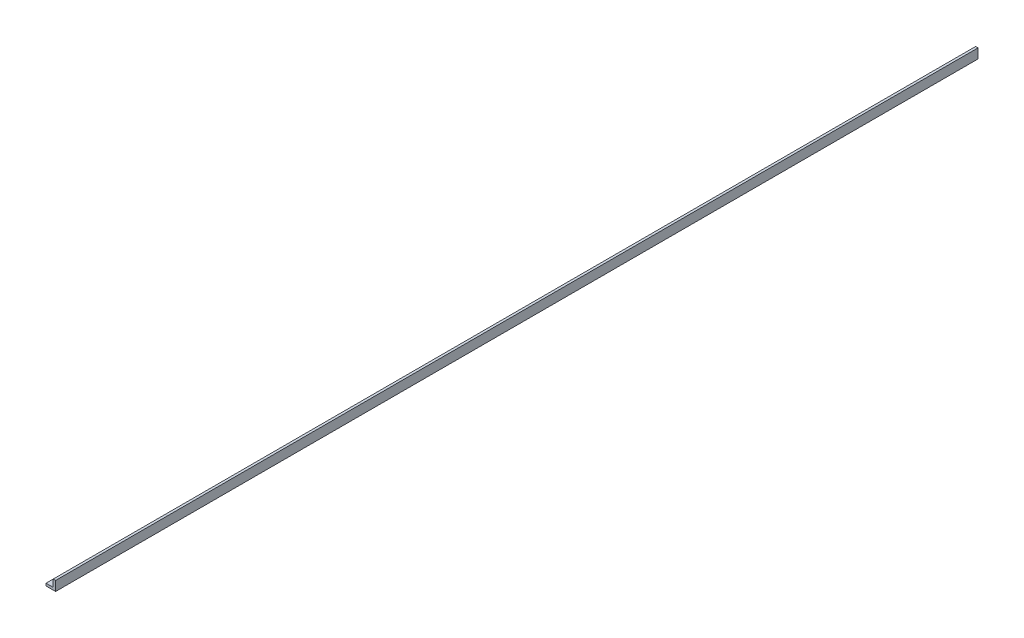
SolidWorks part; units mm, degrees
ref_plane "Front Plane" through (0, 0, 0) normal (0, 0, 1) x (1, 0, 0)
ref_plane "Top Plane" through (0, 0, 0) normal (0, 1, 0) x (1, 0, 0)
ref_plane "Right Plane" through (0, 0, 0) normal (1, 0, 0) x (0, 0, -1)
sketch "Sketch2" plane through (0, 0, 0) normal (0, 0, 1) x (1, 0, 0)
  line L0 (-6.35, 0) -> (6.35, 0)
  line L1 (6.35, 0) -> (6.35, 12.7)
  line L2 (6.35, 12.7) -> (3.175, 12.7)
  line L3 (3.175, 12.7) -> (3.175, 3.175)
  line L4 (3.175, 3.175) -> (-6.35, 3.175)
  line L5 (-6.35, 0) -> (-6.35, 3.175)
  line L6 (4.7625, 12.7) -> (6.35, 12.7) construction
  line L7 (-6.35, 1.5875) -> (-6.35, 0) construction
  dimension "Vert" = 12.7
  dimension "Horz" = 12.7
  dimension "Thickness" = 3.175
extrude "Boss-Extrude1" add sketch "Sketch2" along normal mid plane 1219.2
